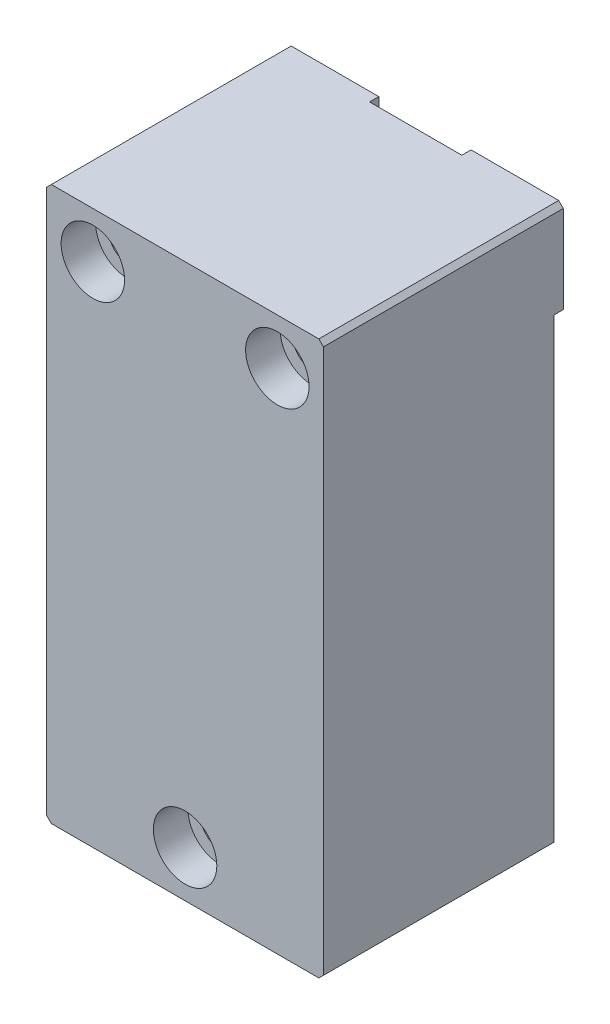
SolidWorks part; units mm, degrees
material "AISI 304"
ref_plane "Front Plane" through (0, 0, 0) normal (0, 0, 1) x (1, 0, 0)
ref_plane "Top Plane" through (0, 0, 0) normal (0, 1, 0) x (1, 0, 0)
ref_plane "Right Plane" through (0, 0, 0) normal (1, 0, 0) x (0, 0, -1)
sketch "Sketch1" plane through (0, 0, 0) normal (0, 0, 1) x (1, 0, 0)
  line L0 (0, -55) -> (0, 55) construction
  line L1 (-38.1, 38.1) -> (38.1, 38.1)
  line L2 (-38.1, 38.1) -> (-38.1, -114.3)
  line L3 (-38.1, -114.3) -> (38.1, -114.3)
  line L4 (38.1, 38.1) -> (38.1, -114.3)
  line L5 (55, 0) -> (-55, 0) construction
  dimension "D1" = 76.2
  dimension "D2" = 152.4
  dimension "D3" = 38.1
  dimension "D4" = 38.1
extrude "Extrude1" add sketch "Sketch1" along normal blind 63.5
sketch "Sketch4" plane through (0, 0, 0) normal (0, 0, -1) x (-1, 0, 0)
  line L0 (38.1, -114.3) -> (-38.1, -114.3) construction
  line L1 (-38.1, 38.1) -> (-12.7, 38.1)
  line L2 (-38.1, 38.1) -> (-38.1, 12.7)
  line L3 (-38.1, 12.7) -> (-12.7, 12.7)
  line L4 (-12.7, 38.1) -> (-12.7, 12.7)
  line L5 (38.1, 38.1) -> (12.7, 38.1)
  line L6 (38.1, 38.1) -> (38.1, 12.7)
  line L7 (38.1, 12.7) -> (12.7, 12.7)
  line L8 (12.7, 38.1) -> (12.7, 12.7)
  line L9 (-12.7, -114.3) -> (12.7, -114.3)
  line L10 (-12.7, -114.3) -> (-12.7, -88.9)
  line L11 (-12.7, -88.9) -> (12.7, -88.9)
  line L12 (12.7, -114.3) -> (12.7, -88.9)
  line L13 (-38.1, -114.3) -> (-38.1, 38.1) construction
  dimension "D1" = 25.4
  dimension "D2" = 25.4
  dimension "D3" = 25.4
  dimension "D4" = 25.4
  dimension "D5" = 25.4
  dimension "D6" = 25.4
  dimension "D7" = 25.4
extrude "Extrude2" add sketch "Sketch4" along normal blind 2.54
hole_wizard "CBORE for 3/8 Socket Head Cap Screw1" positions "Sketch3" profile "Sketch2" counterbore size "3/8" standard "Ansi Inch" end condition through all
sketch "Sketch3" plane through (0, 0, 63.5) normal (0, 0, 1) x (1, 0, 0)
  line L0 (-25.4, 25.4) -> (25.4, 25.4) construction
  line L2 (38.1, 38.1) -> (-38.1, 38.1) construction
  line L3 (-38.1, 38.1) -> (-38.1, -114.3) construction
  line L12 (-38.1, -114.3) -> (38.1, -114.3) construction
  point P0 (-25.4, 25.4)
  point P1 (25.4, 25.4)
  point P5 (0, -101.6)
  dimension "D1" = 12.7
  dimension "D2" = 50.8
  dimension "D3" = 12.7
  dimension "D4" = 38.1
  dimension "D5" = 12.7
sketch "Sketch2" plane through (-25.4, 25.4, 63.5) normal (1, 0, 0) x (0, -1, 0)
  line L0 (0, 0) -> (0, 66.04)
  line L1 (0, 66.04) -> (5.1587, 66.04)
  line L3 (5.1587, 66.04) -> (5.1587, 9.525)
  line L4 (5.1587, 9.525) -> (8.7376, 9.525)
  line L5 (8.7376, 9.525) -> (8.7376, 0)
  line L7 (8.7376, 0) -> (0, 0)
  line L11 (0, -6.35) -> (0, 107.95) construction
  dimension "Thru Hole Dia." = 10.3175
  dimension "Thru Hole Depth" = 66.04
  dimension "C'Bore Dia." = 17.4752
  dimension "C'Bore Depth" = 9.525
chamfer "Chamfer2" distance 1.27 angle 45 8 edges at (0, -114.3, 63.5) (38.1, -38.1, 63.5) (-38.1, -38.1, 63.5) (0, 38.1, 63.5) (38.1, -114.3, 31.75) (-38.1, -114.3, 31.75) (-38.1, 38.1, 30.48) (38.1, 38.1, 30.48)
